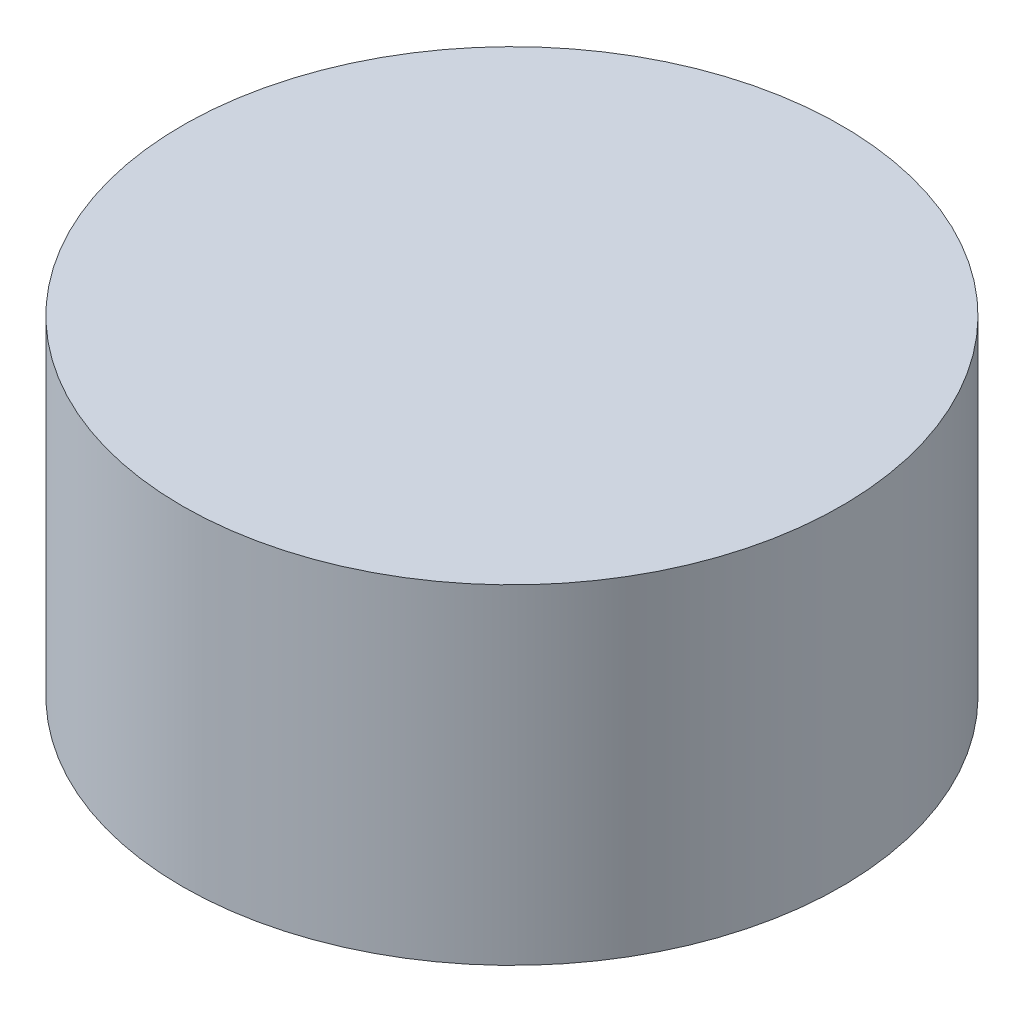
SolidWorks part; units mm, degrees
material "6061-T6 (SS)"
ref_plane "Alzado" through (0, 0, 0) normal (0, 0, 1) x (1, 0, 0)
ref_plane "Planta" through (0, 0, 0) normal (0, 1, 0) x (1, 0, 0)
ref_plane "Vista lateral" through (0, 0, 0) normal (1, 0, 0) x (0, 0, -1)
sketch "Croquis1" plane through (0, 0, 0) normal (0, 1, 0) x (1, 0, 0)
  circle A0 centre (0, 0) radius 3
  dimension "D1" = 6
extrude "Saliente-Extruir1" add sketch "Croquis1" along normal blind 3
